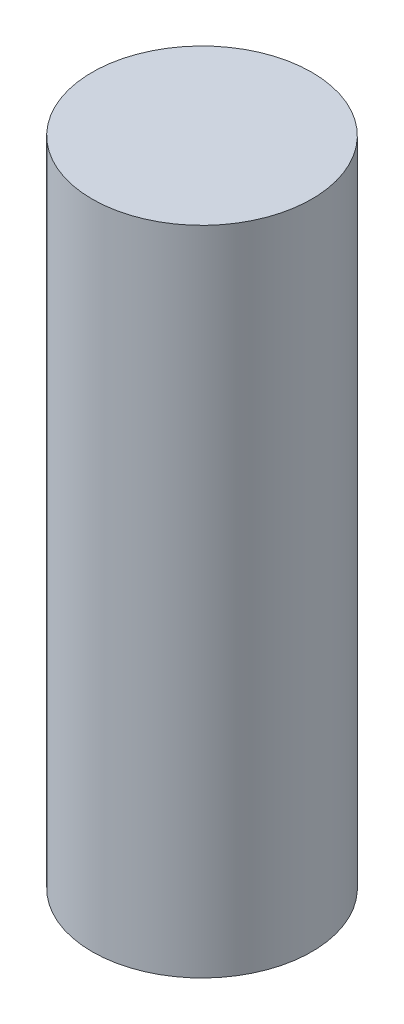
SolidWorks part; units mm, degrees
ref_plane "Front" through (0, 0, 0) normal (0, 0, 1) x (1, 0, 0)
ref_plane "Top" through (0, 0, 0) normal (0, 1, 0) x (1, 0, 0)
ref_plane "Right" through (0, 0, 0) normal (1, 0, 0) x (0, 0, -1)
sketch "Sketch1" plane through (0, 0, 0) normal (0, 1, 0) x (1, 0, 0)
  circle A0 centre (0, 0) radius 3
  dimension "D1" = 6
extrude "Boss-Extrude1" add sketch "Sketch1" along normal blind 17.8
